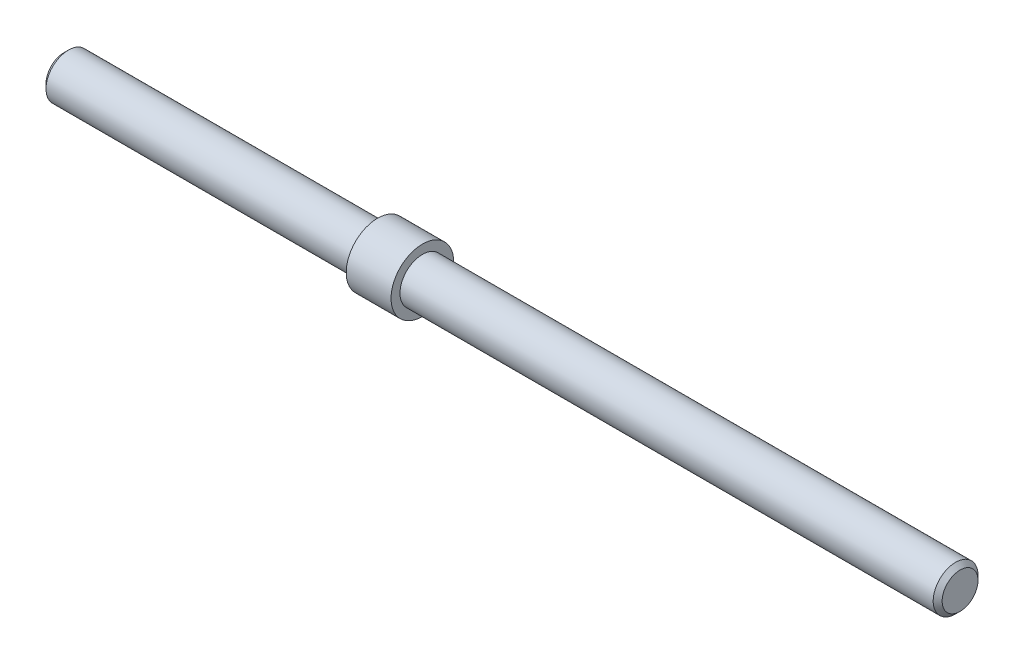
SolidWorks part; units mm, degrees
ref_plane "Front Plane" through (0, 0, 0) normal (0, 0, 1) x (1, 0, 0)
ref_plane "Top Plane" through (0, 0, 0) normal (0, 1, 0) x (1, 0, 0)
ref_plane "Right Plane" through (0, 0, 0) normal (1, 0, 0) x (0, 0, -1)
sketch "Sketch1" plane through (0, 0, 0) normal (1, 0, 0) x (0, 0, -1)
  circle A0 centre (0, 0) radius 5
  dimension "D1" = 10
extrude "Boss-Extrude1" add sketch "Sketch1" along normal blind 200
chamfer "Chamfer1" distance 1 angle 45 2 edges at (200, 0, -5) (0, 0, -5)
sketch "Sketch2" plane through (0, 0, 0) normal (1, 0, 0) x (0, 0, -1)
  circle A0 centre (0, 0) radius 7
  dimension "D1" = 14
extrude "Boss-Extrude3" add sketch "Sketch2" along normal blind 10 from offset 70
